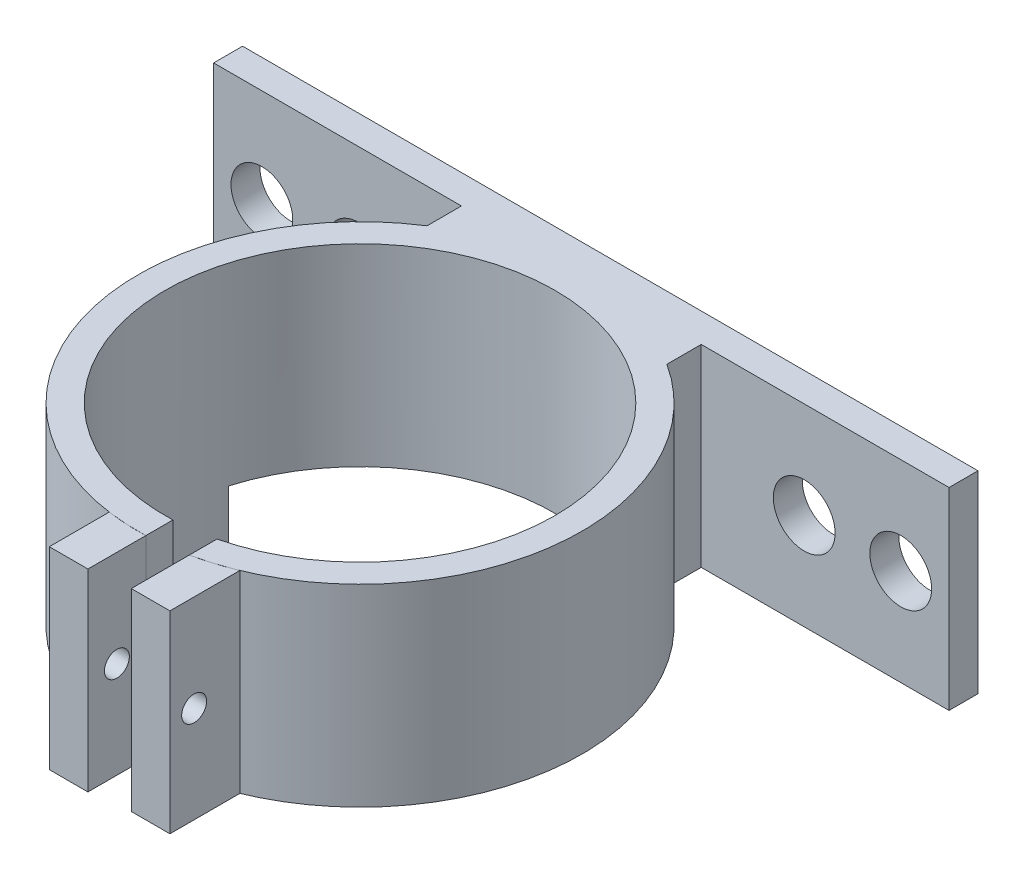
SolidWorks part; units mm, degrees
ref_plane "Front Plane" through (0, 0, 0) normal (0, 0, 1) x (1, 0, 0)
ref_plane "Top Plane" through (0, 0, 0) normal (0, 1, 0) x (1, 0, 0)
ref_plane "Right Plane" through (0, 0, 0) normal (1, 0, 0) x (0, 0, -1)
sketch "Sketch1" plane through (0, 0, 0) normal (0, 1, 0) x (1, 0, 0)
  circle A0 centre (0, 0) radius 11.5
  dimension "D1" = 23
extrude "Boss-Extrude1" add sketch "Sketch1" along normal blind 10
sketch "Sketch5" plane through (0, 10, 0) normal (0, 1, 0) x (1, 0, 0)
  circle A0 centre (0, 0) radius 10.1
  dimension "D1" = 20.2
extrude "Cut-Extrude3" cut sketch "Sketch5" against normal blind 10
sketch "Sketch6" plane through (0, 10, 0) normal (0, 1, 0) x (1, 0, 0)
  line L1 (2.4003, -7.2508) -> (0.4003, -7.2508)
  line L2 (2.4003, -7.2508) -> (2.4003, -12.7541)
  line L3 (2.4003, -12.7541) -> (0.4003, -12.7541)
  line L4 (0.4003, -7.2508) -> (0.4003, -12.7541)
  line L5 (2.4003, -7.2508) -> (0.4003, -12.7541) construction
  line L6 (2.4003, -12.7541) -> (0.4003, -7.2508) construction
  circle A0 centre (0, 0) radius 10.1 construction
  point P0 (1.4003, -10.0025)
  dimension "D1" = 2
  dimension "D2" = 5.5034
extrude "Cut-Extrude4" cut sketch "Sketch6" against normal blind 10
ref_plane "Plane1" through (0.4003, 10, 11.493) normal (0, 1, 0) x (1, 0, 0)
sketch "Sketch7" plane through (0.4003, 10, 11.493) normal (0, 1, 0) x (1, 0, 0)
  line L0 (-2, 0.1048) -> (-2, -3)
  line L2 (0, 0) -> (0, -3)
  line L3 (0, -3) -> (-2, -3)
  arc A0 (0, 0) -> (-2, 0.1048) centre (-0.4003, 11.493) cw
  arc A1 (2, 0.2463) -> (0, 0) centre (-0.4003, 11.493) ccw construction
  dimension "D3" = 11.5
  dimension "D1" = 3
  dimension "D2" = 2
extrude "Boss-Extrude2" add sketch "Sketch7" against normal blind 10 separate body
sketch "Sketch11" plane through (0, 10, 0) normal (0, 1, 0) x (1, 0, 0)
  line L0 (4.4003, -14.2467) -> (4.4003, -10.6248)
  line L2 (2.4003, -11.2467) -> (2.4003, -14.2467)
  line L3 (2.4003, -14.2467) -> (4.4003, -14.2467)
  arc A0 (2.4003, -11.2467) -> (4.4003, -10.6248) centre (0, 0) ccw
  arc A1 (2.4003, -11.2467) -> (0.4003, -11.493) centre (0, 0) ccw construction
  dimension "D3" = 11.5
  dimension "D1" = 2
  dimension "D2" = 3
extrude "Boss-Extrude4" add sketch "Sketch11" against normal blind 10 separate body
sketch "Sketch12" plane through (-1.5997, 0, 0) normal (-1, 0, 0) x (0, 0, 1)
  line L0 (11.3882, 0) -> (14.493, 0) construction
  line L1 (14.493, 0) -> (14.493, 10) construction
  circle A0 centre (12.993, 5) radius 0.645
  dimension "D1" = 1.29
  dimension "D2" = 5
  dimension "D3" = 1.5
extrude "Cut-Extrude5" cut sketch "Sketch12" against normal blind 10
sketch "Sketch16" plane through (0, 0, 0) normal (0, -1, 0) x (1, 0, 0)
  line L6 (-10.1486, 5.1327) -> (-8.6986, 5.1327)
  line L7 (-9.6845, -2.8673) -> (-11.1368, -2.8673)
  arc A0 (0.4003, 10.0921) -> (2.4003, 9.8106) centre (0, 0) ccw construction
  arc A1 (-9.6845, -2.8673) -> (-8.6986, 5.1327) centre (0, 0) cw
  arc A2 (0.4003, 11.493) -> (2.4003, 11.2467) centre (0, 0) ccw construction
  arc A3 (-11.1368, -2.8673) -> (-10.1486, 5.1327) centre (-1.5366, 0.0078) cw
  dimension "D1" = 1.4524
  dimension "D2" = 1.45
extrude "Boss-Extrude7" add sketch "Sketch16" along normal blind 6
sketch "Sketch17" plane through (0, -6, 0) normal (0, -1, 0) x (1, 0, 0)
  line L0 (-11.1368, -2.8673) -> (-9.6845, -2.8673) construction
  line L1 (-10.4106, -2.8673) -> (-6.4106, -2.8673)
  line L2 (-10.4106, -2.8673) -> (-10.4106, 5.1327)
  line L3 (-10.4106, 5.1327) -> (-6.4106, 5.1327)
  line L4 (-6.4106, -2.8673) -> (-6.4106, 5.1327)
  dimension "D1" = 8
  dimension "D2" = 4
extrude "Boss-Extrude8" add sketch "Sketch17" against normal blind 2
sketch "Sketch18" plane through (0, -6, 0) normal (0, -1, 0) x (1, 0, 0)
  line L0 (-11.1368, -2.8673) -> (-6.4106, -2.8673) construction
  line L1 (-6.4106, -2.8673) -> (-6.4106, 5.1327) construction
  circle A0 centre (-8.4106, 1.1327) radius 1.4
  dimension "D1" = 2.8
  dimension "D2" = 4
  dimension "D3" = 2
extrude "Cut-Extrude7" cut sketch "Sketch18" against normal blind 2
sketch "Sketch20" plane through (0, 0, 0) normal (0, -1, 0) x (1, 0, 0)
  line L1 (-0.958, -11.46) -> (19.042, -11.46)
  line L2 (-0.958, -11.46) -> (-0.958, -12.96)
  line L3 (-0.958, -12.96) -> (19.042, -12.96)
  line L4 (19.042, -11.46) -> (19.042, -12.96)
  arc A0 (-11.1368, -2.8673) -> (2.4003, 11.2467) centre (0, 0) ccw construction
  dimension "D1" = 20
  dimension "D2" = 1.5
extrude "Boss-Extrude10" add sketch "Sketch20" against normal blind 10
mirror "Mirror1" about plane through (0, 0, 0) normal (1, 0, 0) of "Boss-Extrude10"
sketch "Sketch26" plane through (0, 0, -12.96) normal (0, 0, -1) x (-1, 0, 0)
  line L0 (-19.042, 10) -> (-19.042, 0) construction
  line L1 (19.042, 0) -> (-19.042, 0) construction
  circle A0 centre (-16.542, 5) radius 1.6
  dimension "D1" = 3.2
  dimension "D3" = 5
  dimension "D2" = 2.5
extrude "Cut-Extrude14" cut sketch "Sketch26" against normal blind 10
mirror "Mirror2" about plane through (0, 0, 0) normal (1, 0, 0) of "Cut-Extrude14"
sketch "Sketch27" plane through (0, 0, -12.96) normal (0, 0, -1) x (-1, 0, 0)
  line L0 (19.042, 0) -> (-19.042, 0) construction
  circle A0 centre (-11.542, 5) radius 1.6
  circle A1 centre (-16.542, 5) radius 1.6 construction
  dimension "D1" = 3.2
  dimension "D2" = 5
  dimension "D3" = 5
extrude "Cut-Extrude15" cut sketch "Sketch27" against normal blind 2
mirror "Mirror3" about plane through (0, 0, 0) normal (1, 0, 0) of "Cut-Extrude15"
sketch "Sketch28" plane through (0, 0, 0) normal (0, -1, 0) x (1, 0, 0)
  line L0 (0, -11.4419) -> (-6.2096, -9.1373)
  line L1 (-6.2096, -9.1373) -> (-6.2096, -12.3381)
  line L2 (-6.2096, -12.3381) -> (0, -11.4419)
extrude "Boss-Extrude11" add sketch "Sketch28" against normal blind 10
mirror "Mirror4" about plane through (0, 0, 0) normal (1, 0, 0) of "Boss-Extrude11"
